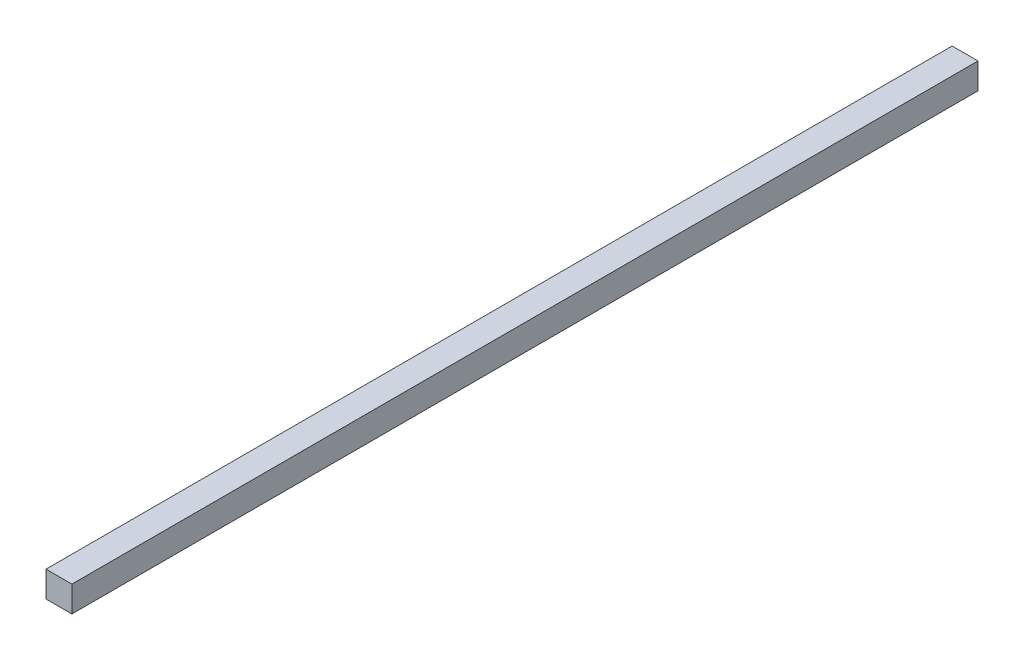
SolidWorks part; units mm, degrees
ref_plane "Front" through (0, 0, 0) normal (0, 0, 1) x (1, 0, 0)
ref_plane "Top" through (0, 0, 0) normal (0, 1, 0) x (1, 0, 0)
ref_plane "Right" through (0, 0, 0) normal (1, 0, 0) x (0, 0, -1)
sketch "Sketch2" plane through (0, 0, 0) normal (0, 0, 1) x (1, 0, 0)
  line L1 (-5, -5) -> (5, -5)
  line L2 (-5, -5) -> (-5, 5)
  line L3 (-5, 5) -> (5, 5)
  line L4 (5, -5) -> (5, 5)
  line L5 (-5, -5) -> (5, 5) construction
  line L6 (-5, 5) -> (5, -5) construction
  point P0 (0, 0)
  dimension "D1" = 10
  dimension "D2" = 10
extrude "Boss-Extrude1" add sketch "Sketch2" along normal blind 350
